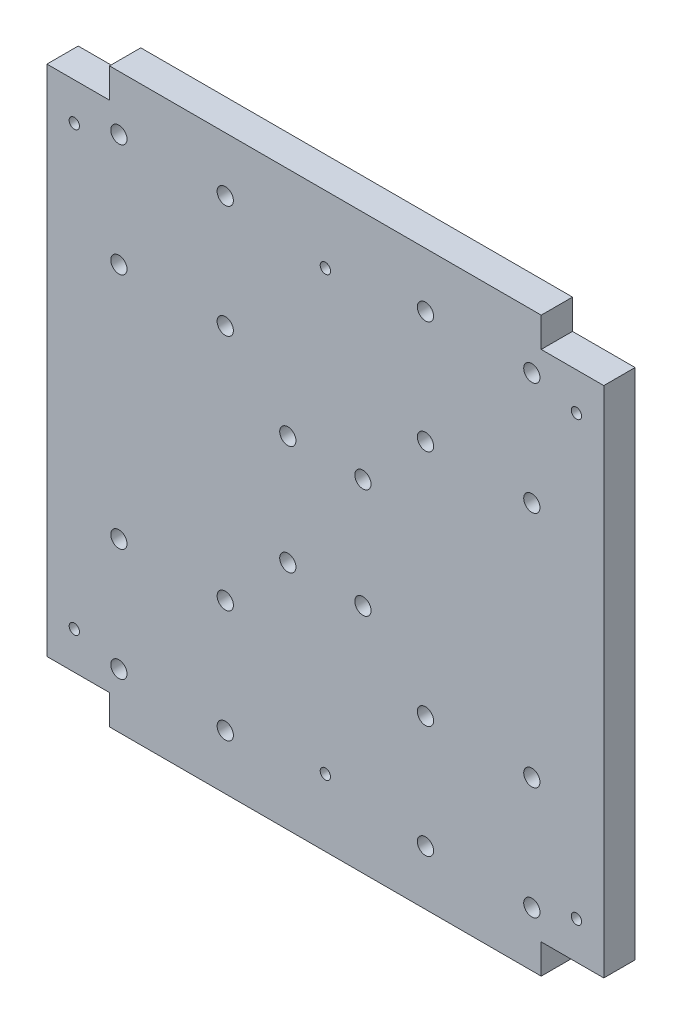
SolidWorks part; units mm, degrees
ref_plane "Front Plane" through (0, 0, 0) normal (0, 0, 1) x (1, 0, 0)
ref_plane "Top Plane" through (0, 0, 0) normal (0, 1, 0) x (1, 0, 0)
ref_plane "Right Plane" through (0, 0, 0) normal (1, 0, 0) x (0, 0, -1)
sketch "Sketch1" plane through (0, 0, 0) normal (0, 0, 1) x (1, 0, 0)
  line L0 (0, 91.5) -> (0, -91.5) construction
  line L2 (-89, 82) -> (-89, -82)
  line L3 (-89, -82) -> (-69, -82)
  line L4 (89, 82) -> (89, -82)
  line L5 (-89, 82) -> (89, -82) construction
  line L6 (-89, -82) -> (89, 82) construction
  line L7 (-69, 91.5) -> (69, 91.5)
  line L8 (-69, 91.5) -> (-69, 82)
  line L10 (69, 91.5) -> (69, 82)
  line L11 (-89, 0) -> (89, 0) construction
  line L12 (69, -91.5) -> (69, -82)
  line L14 (-69, -91.5) -> (-69, -82)
  line L15 (-69, -91.5) -> (69, -91.5)
  line L16 (-89, 82) -> (-69, 82)
  line L17 (69, -82) -> (89, -82)
  line L18 (69, 82) -> (89, 82)
  circle A0 centre (-66, 74) radius 2.6
  circle A1 centre (-32, 74) radius 2.6
  circle A2 centre (-32, 38) radius 2.6
  circle A3 centre (-66, 38) radius 2.6
  circle A4 centre (66, 38) radius 2.6
  circle A5 centre (32, 38) radius 2.6
  circle A6 centre (32, 74) radius 2.6
  circle A7 centre (66, 74) radius 2.6
  circle A8 centre (66, -74) radius 2.6
  circle A9 centre (32, -74) radius 2.6
  circle A10 centre (32, -38) radius 2.6
  circle A11 centre (66, -38) radius 2.6
  circle A12 centre (-66, -38) radius 2.6
  circle A13 centre (-32, -38) radius 2.6
  circle A14 centre (-32, -74) radius 2.6
  circle A15 centre (-66, -74) radius 2.6
  circle A16 centre (-12, 17.5) radius 2.6
  circle A17 centre (12, 17.5) radius 2.6
  circle A18 centre (12, -17.5) radius 2.6
  circle A19 centre (-12, -17.5) radius 2.6
  point P0 (0, 0)
  dimension "D6" = 5.2
  dimension "D8" = 23
  dimension "D11" = 2
  dimension "D12" = 2
  dimension "D13" = 5.2
  dimension "D1" = 178
  dimension "D3" = 138
  dimension "D4" = 9.5
  dimension "D9" = 2
  dimension "D10" = 2
extrude "Boss-Extrude3" add sketch "Sketch1" along normal blind 10
hole_wizard "M4 Tapped Hole1" positions "Sketch2" profile "Sketch3" tap size "M4" standard "ISO" end condition through all
sketch "Sketch2" plane through (0, 0, 10) normal (0, 0, 1) x (1, 0, 0)
  line L1 (-89, 82) -> (-89, -82) construction
  line L2 (0, 91.5) -> (0, -91.5) construction
  line L6 (-89, 0) -> (89, 0) construction
  line L7 (89, -82) -> (89, 82) construction
  line L8 (-69, 82) -> (-89, 82) construction
  line L10 (69, 91.5) -> (-69, 91.5) construction
  line L11 (-69, -91.5) -> (69, -91.5) construction
  point P0 (-80.25, 70)
  point P21 (80.25, 70)
  point P22 (0, 70)
  point P25 (0, -70)
  point P26 (80.25, -70)
  point P27 (-80.25, -70)
  dimension "D1" = 12
  dimension "D2" = 8.75
sketch "Sketch3" plane through (-80.25, 70, 10) normal (1, 0, 0) x (0, -1, 0)
  line L0 (0, 0) -> (0, 10)
  line L1 (0, 10) -> (1.65, 10)
  line L2 (1.65, 10) -> (1.65, 0)
  line L5 (1.65, 0) -> (0, 0)
  line L11 (0, -6.35) -> (0, 107.95) construction
  dimension "Thru Tap Drill Dia." = 3.3
  dimension "Thru Tap Drill Depth" = 10
cosmetic thread "Hole Thread1" parameters "D2"=4
cosmetic thread "Hole Thread2" parameters "D2"=4
cosmetic thread "Hole Thread3" parameters "D2"=4
cosmetic thread "Hole Thread4" parameters "D2"=4
cosmetic thread "Hole Thread5" parameters "D2"=4
cosmetic thread "Hole Thread6" parameters "D2"=4
